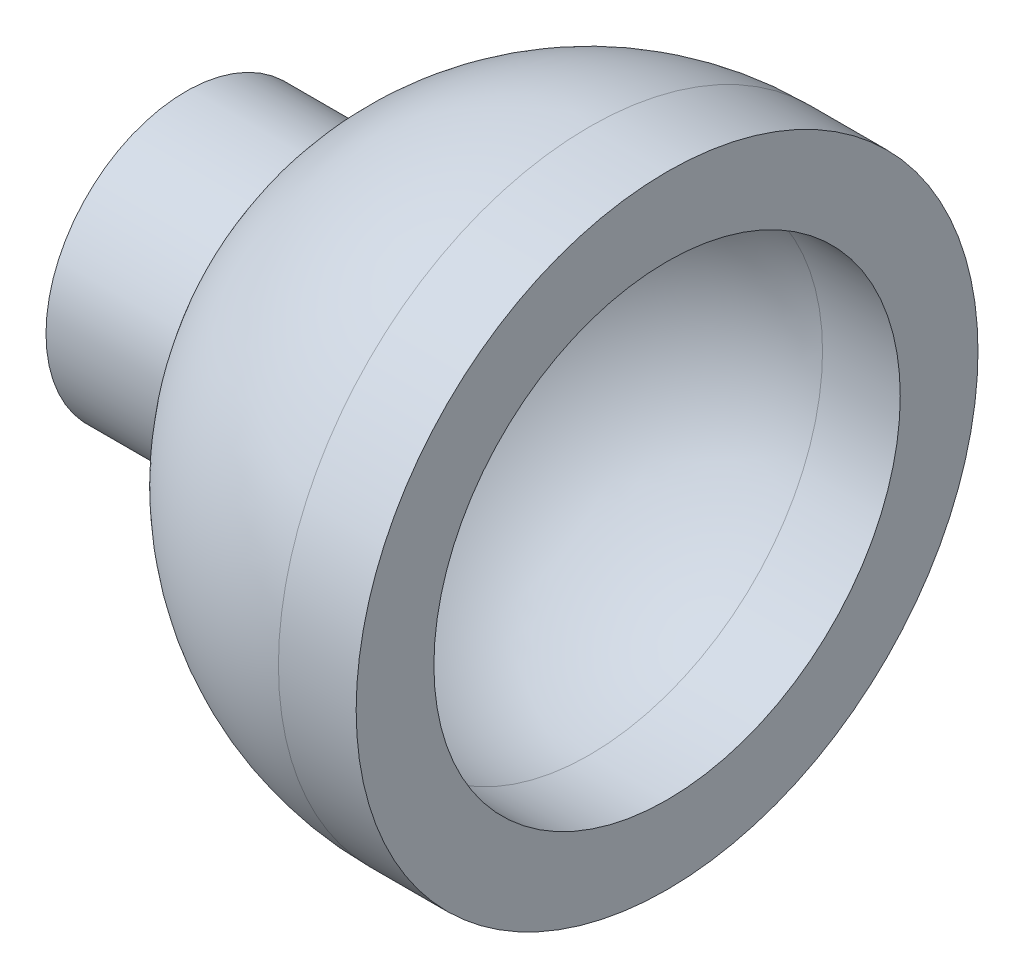
SolidWorks part; units mm, degrees
ref_plane "Front Plane" through (0, 0, 0) normal (0, 0, 1) x (1, 0, 0)
ref_plane "Top Plane" through (0, 0, 0) normal (0, 1, 0) x (1, 0, 0)
ref_plane "Right Plane" through (0, 0, 0) normal (1, 0, 0) x (0, 0, -1)
sketch "Sketch1" plane through (0, 0, 0) normal (0, 0, 1) x (1, 0, 0)
  line L0 (-14.8397, 0) -> (14.1274, 0) construction
  line L2 (-10.3803, 1.6) -> (-7.8384, 1.6)
  line L3 (-10.3803, 3.6) -> (-7.1442, 3.6)
  line L4 (-10.3803, 1.6) -> (-10.3803, 3.6)
  line L7 (-7.8384, 1.6) -> (-5.7827, 1.6)
  line L8 (-10.3803, 3.6) -> (-5.8095, 3.6) construction
  line L9 (-10.3803, 1.6) -> (-5.8095, 1.6) construction
  line L10 (0, 8) -> (2, 8)
  line L11 (2, 8) -> (2, 6)
  line L12 (2, 6) -> (0, 6)
  arc A0 (0, 6) -> (-5.7827, 1.6) centre (0, 0) ccw
  arc A1 (0, 8) -> (-7.1442, 3.6) centre (0, 0) ccw
  circle A3 centre (0, 0) radius 8 construction
  circle A4 centre (0, 0) radius 6 construction
  point P6 (5.7378, 1.7542)
  point P9 (8, 0)
  dimension "D1" = 12
  dimension "D3" = 3.2
  dimension "D5" = 2
  dimension "D2" = 2
  dimension "D4" = 2
revolve "Revolve1" add sketch "Sketch1" angle 360 about L0
